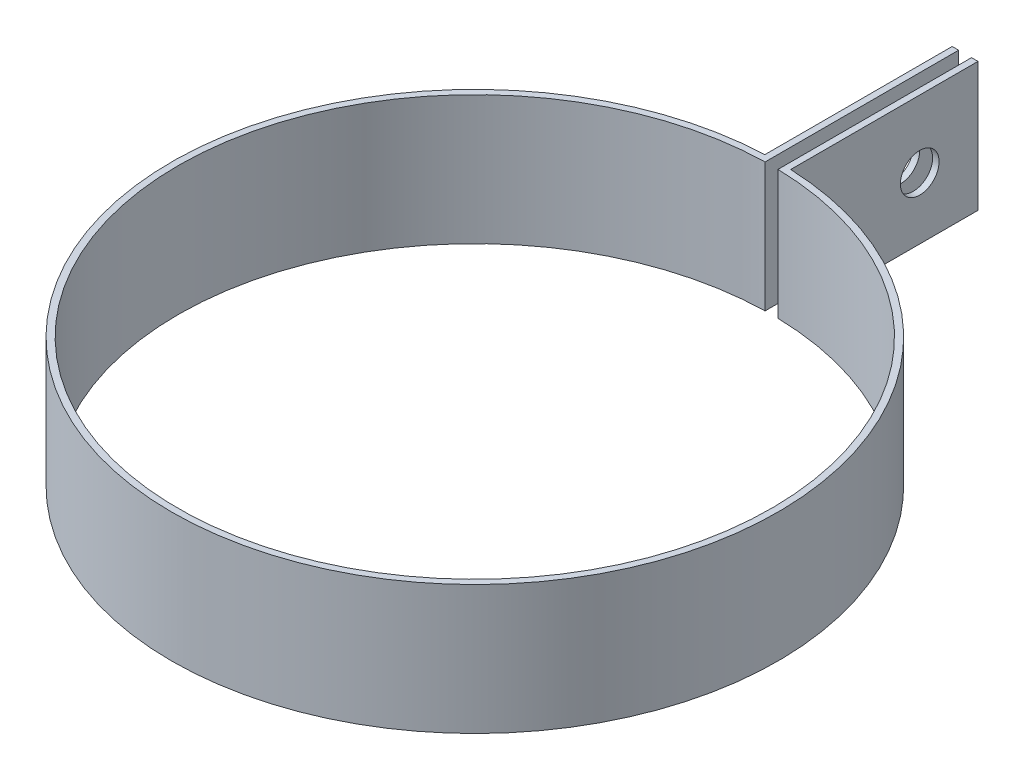
SolidWorks part; units mm, degrees
ref_plane "Front Plane" through (0, 0, 0) normal (0, 0, 1) x (1, 0, 0)
ref_plane "Top Plane" through (0, 0, 0) normal (0, 1, 0) x (1, 0, 0)
ref_plane "Right Plane" through (0, 0, 0) normal (1, 0, 0) x (0, 0, -1)
sketch "Sketch1" plane through (0, 0, 0) normal (0, 1, 0) x (1, 0, 0)
  line L0 (-0.5, 37.9946) -> (-0.5, 22.9946)
  line L1 (0.5, 37.9946) -> (0.5, 22.9946)
  line L2 (-1, 37.9946) -> (-1, 23.4787)
  line L3 (1, 37.9946) -> (1, 23.4787)
  line L4 (-1, 37.9946) -> (-0.5, 37.9946)
  line L5 (0.5, 37.9946) -> (1, 37.9946)
  arc A0 (-0.5, 22.9946) -> (0.5, 22.9946) centre (0, 0) ccw
  arc A1 (-1, 23.4787) -> (1, 23.4787) centre (0, 0) ccw
  dimension "D1" = 0.5
  dimension "D8" = 23
  dimension "D2" = 0.5
  dimension "D3" = 15
  dimension "D4" = 15
  dimension "D6" = 0.5
  dimension "D7" = 0.5
  dimension "D5" = 0.5
extrude "Boss-Extrude1" add sketch "Sketch1" along normal blind 10
sketch "Sketch2" plane through (1, 0, 0) normal (1, 0, 0) x (0, 0, -1)
  line L0 (23.4787, 10) -> (23.4787, 0) construction
  circle A0 centre (33.4787, 4.783) radius 1.5
  dimension "D2" = 3
  dimension "D1" = 10
extrude "Cut-Extrude1" cut sketch "Sketch2" against normal through all
